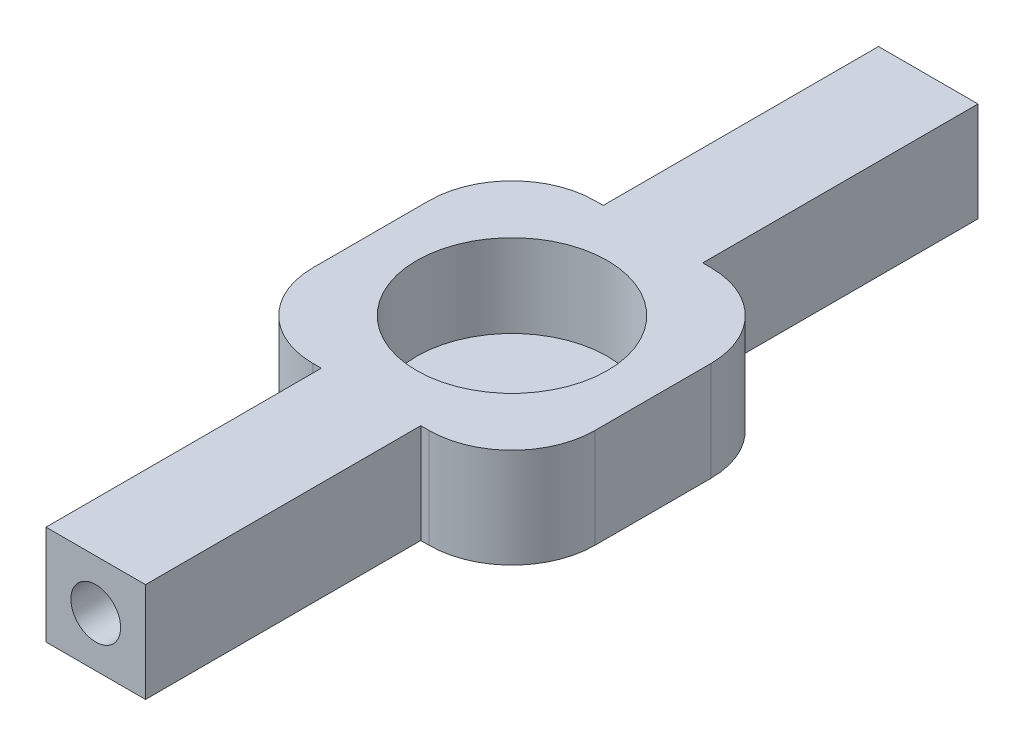
SolidWorks part; units mm, degrees
ref_plane "Front Plane" through (0, 0, 0) normal (0, 0, 1) x (1, 0, 0)
ref_plane "Top Plane" through (0, 0, 0) normal (0, 1, 0) x (1, 0, 0)
ref_plane "Right Plane" through (0, 0, 0) normal (1, 0, 0) x (0, 0, -1)
sketch "Sketch1" plane through (0, 0, 0) normal (0, 1, 0) x (1, 0, 0)
  line L0 (0, 0) -> (0, 8.5) construction
  line L4 (0, 0) -> (-8.5, 0) construction
  line L5 (8.5, 8.5) -> (3, 8.5)
  line L6 (-8.5, 8.5) -> (-8.5, -8.5)
  line L7 (8.5, 8.5) -> (8.5, -8.5)
  line L8 (8.5, -8.5) -> (3, -8.5)
  line L9 (0, 8.5) -> (0, 25.1) construction
  line L10 (-3, 25.1) -> (3, 25.1)
  line L11 (3, 25.1) -> (3, 8.5)
  line L12 (-3, 25.1) -> (-3, 8.5)
  line L13 (3, -25.1) -> (3, -8.5)
  line L14 (-3, -25.1) -> (3, -25.1)
  line L15 (-3, -25.1) -> (-3, -8.5)
  line L16 (-3, 8.5) -> (-8.5, 8.5)
  line L17 (-3, -8.5) -> (-8.5, -8.5)
  circle A0 centre (0, 0) radius 5.75
  point P3 (0, 0)
  point P11 (9.0849, 2.7775)
  point P12 (8.5, 0)
  dimension "D1" = 8.5
  dimension "D2" = 8.5
  dimension "D3" = 16.6
  dimension "D4" = 3
extrude "Boss-Extrude1" add sketch "Sketch1" along normal blind 6 contours A0 | L8 L13 L14 L15 L17 L6 L16 L12 L10 L11 L5 L7
sketch "Sketch8" plane through (0, 0, 0) normal (0, -1, 0) x (1, 0, 0)
  line L1 (-8.5, 8.5) -> (8.5, 8.5)
  line L2 (-8.5, 8.5) -> (-8.5, -8.5)
  line L3 (-8.5, -8.5) -> (8.5, -8.5)
  line L4 (8.5, 8.5) -> (8.5, -8.5)
extrude "Boss-Extrude6" add sketch "Sketch8" against normal blind 1 contours L2 L1 L4 L3
fillet "Fillet1" radius 5 4 edges at (8.5, 3, 8.5) (-8.5, 3, 8.5) (8.5, 3, -8.5) (-8.5, 3, -8.5)
sketch "Sketch9" plane through (0, 0, -25.1) normal (0, 0, -1) x (-1, 0, 0)
  line L0 (0, 6) -> (0, 0) construction
  line L1 (3, 6) -> (-3, 6) construction
  circle A0 centre (0, 3) radius 1.5
extrude "Cut-Extrude2" cut sketch "Sketch9" against normal blind 5
sketch "Sketch10" plane through (0, 0, 25.1) normal (0, 0, 1) x (1, 0, 0)
  line L0 (0, 6) -> (0, 0) construction
  line L1 (-3, 6) -> (3, 6) construction
  line L2 (-3, 0) -> (3, 0) construction
  circle A0 centre (0, 3) radius 1.5
extrude "Cut-Extrude3" cut sketch "Sketch10" against normal blind 5
